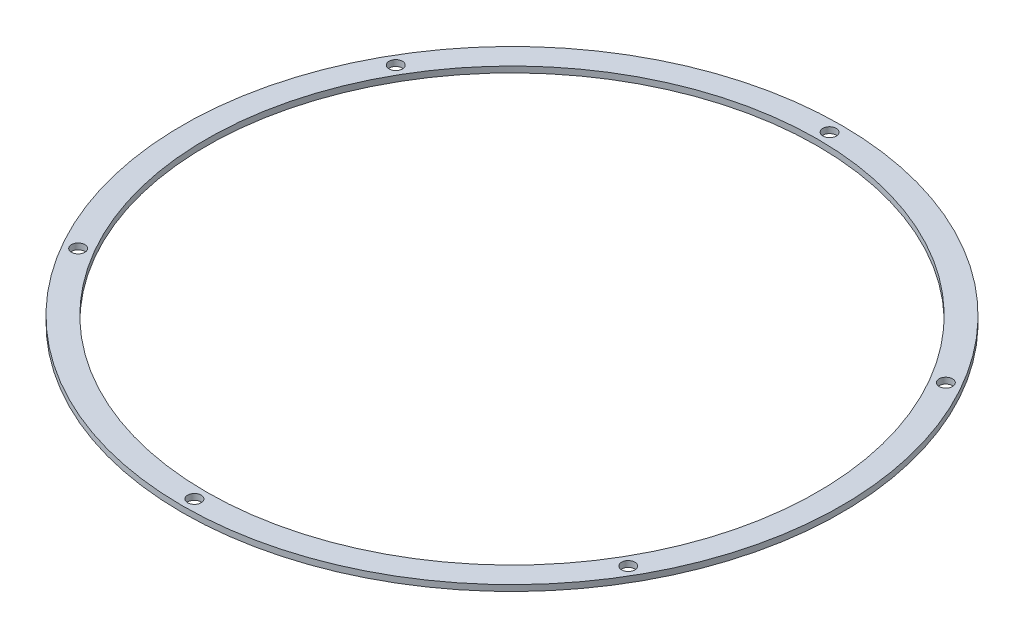
SolidWorks part; units mm, degrees
material "ABS PC"
ref_plane "Front Plane" through (0, 0, 0) normal (0, 0, 1) x (1, 0, 0)
ref_plane "Top Plane" through (0, 0, 0) normal (0, 1, 0) x (1, 0, 0)
ref_plane "Right Plane" through (0, 0, 0) normal (1, 0, 0) x (0, 0, -1)
sketch "Sketch1" plane through (0, 0, 0) normal (0, 1, 0) x (1, 0, 0)
  line L0 (0, 168.5) -> (0, 0) construction
  line L1 (0, 174.85) -> (0, 162.15) construction
  line L2 (0, -55) -> (0, 55) construction
  circle A0 centre (0, 0) radius 168.5 construction
  circle A1 centre (0, 168.5) radius 3.556
  circle A2 centre (145.9253, 84.25) radius 3.556
  circle A3 centre (145.9253, -84.25) radius 3.556
  circle A4 centre (0, -168.5) radius 3.556
  circle A5 centre (-145.9253, -84.25) radius 3.556
  circle A6 centre (-145.9253, 84.25) radius 3.556
  circle A7 centre (0, 0) radius 174.85
  circle A8 centre (0, 0) radius 162.15
  point P17 (0, 0)
  point P20 (0, 168.5)
  dimension "D1" = 7.112
  dimension "D2" = 337
  dimension "D6" = 12.7
  dimension "D4" = 60
  dimension "D5" = 60
  dimension "D3" = 6
extrude "Boss-Extrude1" add sketch "Sketch1" along normal blind 3.175
